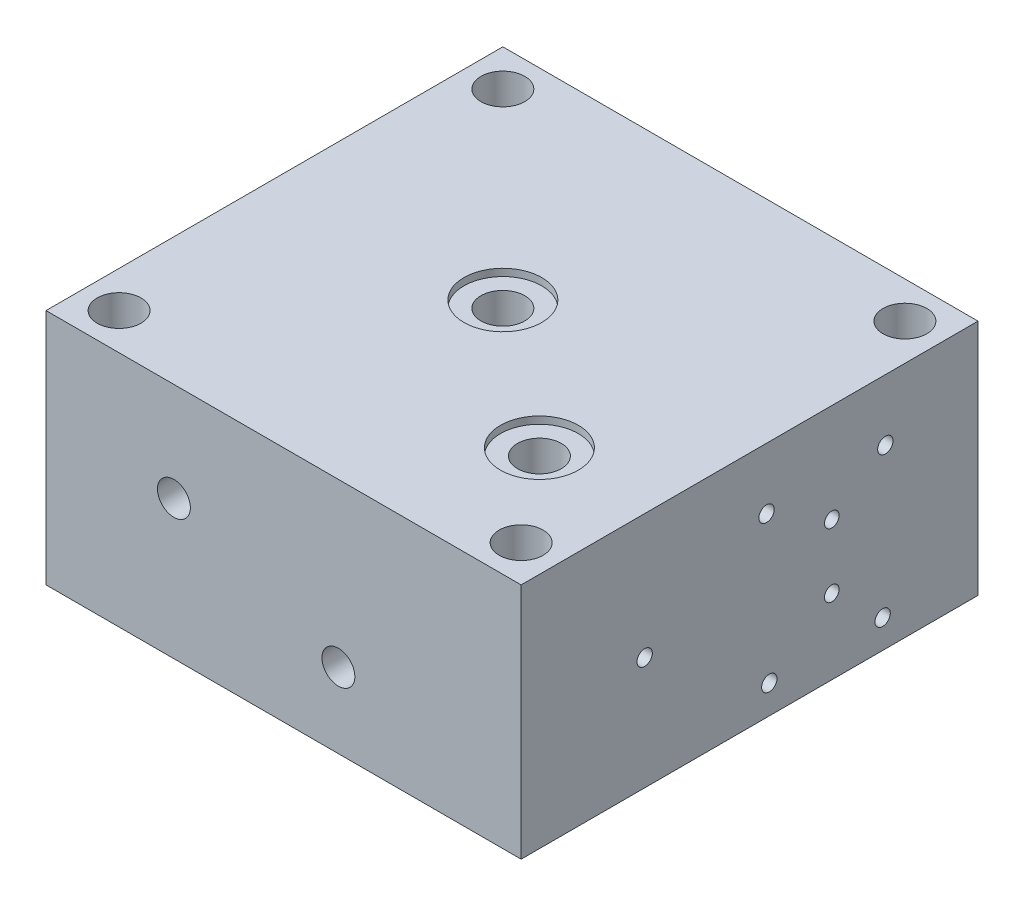
SolidWorks part; units mm, degrees
ref_plane "前视基准面" through (0, 0, 0) normal (0, 0, 1) x (1, 0, 0)
ref_plane "上视基准面" through (0, 0, 0) normal (0, 1, 0) x (1, 0, 0)
ref_plane "右视基准面" through (0, 0, 0) normal (1, 0, 0) x (0, 0, -1)
sketch "草图2" plane through (0, 0, 0) normal (0, 1, 0) x (1, 0, 0)
  line L1 (-65, -62.5) -> (65, -62.5)
  line L2 (-65, -62.5) -> (-65, 62.5)
  line L3 (-65, 62.5) -> (65, 62.5)
  line L4 (65, -62.5) -> (65, 62.5)
  line L5 (-65, -62.5) -> (65, 62.5) construction
  line L6 (-65, 62.5) -> (65, -62.5) construction
  circle A0 centre (-55, 52.5) radius 6
  circle A1 centre (55, 52.5) radius 6
  circle A2 centre (55, -52.5) radius 6
  circle A3 centre (-55, -52.5) radius 6
  point P0 (0, 0)
  dimension "D1" = 10
  dimension "D2" = 10
  dimension "D3" = 2
  dimension "D4" = 2
extrude "凸台-拉伸1" add sketch "草图2" along normal blind 65 contours A2 | A3 | A1 | L2 L3 L4 L1 | A0
sketch "草图19" plane through (-65, 0, 0) normal (-1, 0, 0) x (0, 0, 1)
  line L0 (-62.5, 65) -> (-62.5, 38)
  line L1 (-62.5, 65) -> (-62.5, 0) construction
  line L2 (-62.5, 38) -> (-22.5, 38)
sketch "草图21" plane through (0, 0, -62.5) normal (0, 0, -1) x (-1, 0, 0)
  point P10 (-4.7, 9.8)
  point P11 (-12.2, 20.5)
  point P12 (-30.5, 9.8)
  point P13 (-23, 20.5)
  point P22 (-30.5, 31.2)
  point P23 (-4.7, 31.2)
  point P24 (-32.5, 20.5)
  point P25 (-17.6, 30.4)
  dimension "D3" = 27.8
  dimension "D4" = 12.9
  dimension "D5" = 10.7
  dimension "D6" = 20.6
  dimension "D7" = 21.4
  dimension "D8" = 25.8
  dimension "D1" = 7.5
  dimension "D2" = 18.3
sketch "草图26" plane through (65, 0, 0) normal (1, 0, 0) x (0, 0, -1)
  point P2 (-28.7046, 20.5)
  point P8 (5.4, 7.8)
  point P9 (4.65, 48.3)
  point P10 (37.15, 48.3)
  point P11 (36.4, 7.8)
  point P12 (22.4954, 38)
  point P13 (22.4954, 20.5)
  dimension "D1" = 40.5
  dimension "D2" = 0.75
  dimension "D3" = 31
  dimension "D4" = 31.75
  dimension "D5" = 30.2
  dimension "D6" = 12.7
hole_wizard "M5 螺纹孔3" positions "3D草图11" profile "草图27" tap size "M5" standard "GB"
sketch3d "3D草图11"
  point P0 (65, 48.3, -4.65)
  point P3 (65, 48.3, -37.15)
  point P6 (65, 7.8, -36.4)
  point P9 (65, 7.8, -5.4)
sketch "草图27" plane through (65, 48.3, -4.65) normal (0, 1, 0) x (0, 0, -1)
  line L0 (0, 0) -> (0, 13.2618)
  line L1 (0, 13.2618) -> (2.1, 12)
  line L2 (2.1, 12) -> (2.1, 0)
  line L5 (2.1, 0) -> (0, 0)
  line L10 (0, 13.2618) -> (-2.1, 12) construction
  line L11 (0, -6.35) -> (0, 107.95) construction
  dimension "螺纹孔钻头直径" = 4.2
  dimension "螺纹孔钻头深度" = 12
  dimension "导头角度" = 118
cosmetic thread "孔螺蚊线9" parameters "D1"=8, "D2"=5
cosmetic thread "孔螺蚊线10" parameters "D1"=8, "D2"=5
cosmetic thread "孔螺蚊线11" parameters "D1"=8, "D2"=5
cosmetic thread "孔螺蚊线12" parameters "D1"=8, "D2"=5
hole_wizard "Ø4.0 (4) 直径孔9" positions "3D草图12" profile "草图28" hole size "Ø4.0" standard "GB"
sketch3d "3D草图12"
  point P0 (65, 20.5, -22.4954)
sketch "草图28" plane through (65, 20.5, -22.4954) normal (0, 1, 0) x (0, 0, -1)
  line L0 (0, 0) -> (0, 33.7017)
  line L1 (0, 33.7017) -> (2, 32.5)
  line L2 (2, 32.5) -> (2, 0)
  line L5 (2, 0) -> (0, 0)
  line L10 (0, 33.7017) -> (-2, 32.5) construction
  line L11 (0, -6.35) -> (0, 107.95) construction
  dimension "孔直径" = 4
  dimension "孔深度" = 32.5
  dimension "导头角度" = 118
hole_wizard "Ø6.0 (6) 直径孔1" positions "3D草图13" profile "草图31" hole size "Ø6.0" standard "GB"
sketch3d "3D草图13"
  point P0 (32.5, 20.5, -62.5)
sketch "草图31" plane through (32.5, 20.5, -62.5) normal (1, 0, 0) x (0, 1, 0)
  line L0 (0, 0) -> (0, 43.8026)
  line L1 (0, 43.8026) -> (3, 42)
  line L2 (3, 42) -> (3, 0)
  line L5 (3, 0) -> (0, 0)
  line L10 (0, 43.8026) -> (-3, 42) construction
  line L11 (0, -6.35) -> (0, 107.95) construction
  dimension "孔直径" = 6
  dimension "孔深度" = 42
  dimension "导头角度" = 118
sketch "草图38" plane through (-65, 0, 0) normal (-1, 0, 0) x (0, 0, 1)
  point P0 (-22.5, 38)
  point P1 (-37, 52.5)
  point P6 (-8, 52.5)
  point P7 (-8, 23.5)
  point P8 (-37, 23.5)
  dimension "D1" = 14.5
  dimension "D2" = 14.5
  dimension "D3" = 2
  dimension "D4" = 2
sketch "草图40" plane through (0, 0, 62.5) normal (0, 0, 1) x (1, 0, 0)
  line L0 (-65, 38) -> (-30, 38)
hole_wizard "Ø4.0 (4) 直径孔11" positions "3D草图17" profile "草图41" hole size "Ø4.0" standard "GB"
sketch3d "3D草图17"
  point P0 (-30, 38, 62.5)
sketch "草图41" plane through (-30, 38, 62.5) normal (1, 0, 0) x (0, -1, 0)
  line L0 (0, 0) -> (0, 86.2017)
  line L1 (0, 86.2017) -> (2, 85)
  line L2 (2, 85) -> (2, 0)
  line L5 (2, 0) -> (0, 0)
  line L10 (0, 86.2017) -> (-2, 85) construction
  line L11 (0, -6.35) -> (0, 107.95) construction
  dimension "孔直径" = 4
  dimension "孔深度" = 85
  dimension "导头角度" = 118
hole_wizard "M10x1.0 螺纹孔1" positions "3D草图18" profile "草图42" tap size "M10x1.0" standard "GB"
sketch3d "3D草图18"
  point P0 (-30, 38, 62.5)
sketch "草图42" plane through (-30, 38, 62.5) normal (1, 0, 0) x (0, -1, 0)
  line L0 (0, 0) -> (0, 15.7039)
  line L1 (0, 15.7039) -> (4.5, 13)
  line L2 (4.5, 13) -> (4.5, 0)
  line L5 (4.5, 0) -> (0, 0)
  line L10 (0, 15.7039) -> (-4.5, 13) construction
  line L11 (0, -6.35) -> (0, 107.95) construction
  dimension "螺纹孔钻头直径" = 9
  dimension "螺纹孔钻头深度" = 13
  dimension "导头角度" = 118
cosmetic thread "孔螺蚊线17" parameters "D1"=8, "D2"=10
sketch "草图44" plane through (0, 0, 62.5) normal (0, 0, 1) x (1, 0, 0)
  line L0 (65, 0) -> (17.6, 0)
  line L1 (-65, 0) -> (65, 0) construction
  line L2 (17.6, 0) -> (17.6, 30.4)
sketch "草图46" plane through (0, 65, 0) normal (0, 1, 0) x (1, 0, 0)
  line L0 (65, -62.5) -> (35, -62.5)
  line L1 (65, -62.5) -> (17.6, -62.5) construction
  line L2 (35, -62.5) -> (35, -27.5)
  line L3 (65, 62.5) -> (-5, 62.5)
  line L4 (-65, 62.5) -> (65, 62.5) construction
  line L5 (-5, 62.5) -> (-5, -7.5)
sketch "草图50" plane through (0, 0, 0) normal (0, -1, 0) x (-1, 0, 0)
  line L0 (65, 62.5) -> (-23, 62.5)
  line L1 (65, 62.5) -> (-65, 62.5) construction
  line L2 (-23, 62.5) -> (-23, 3.7)
sketch "草图52" plane through (0, 0, -62.5) normal (0, 0, -1) x (-1, 0, 0)
  line L0 (-32.5, 20.5) -> (-23.7, 20.5)
  line L1 (-23.7, 20.5) -> (-23.7, 10.1)
  line L2 (-23.7, 20.5) -> (-23.7, 30.9)
  line L3 (-23.7, 20.5) -> (-15, 20.5)
  line L4 (-32.5, 20.5) -> (-32.5, 36)
  line L5 (-32.5, 36) -> (-45.2, 36)
  line L6 (-45.2, 36) -> (-4.7, 36)
  line L8 (-4.7, 36) -> (-4.7, 5)
  line L9 (-45.2, 36) -> (-45.2, 5)
  point P4 (0, 0)
hole_wizard "M5 螺纹孔5" positions "3D草图25" profile "草图53" tap size "M5" standard "GB"
sketch3d "3D草图25"
  point P0 (4.7, 36, -62.5)
  point P3 (45.2, 36, -62.5)
  point P6 (45.2, 5, -62.5)
  point P9 (4.7, 5, -62.5)
sketch "草图53" plane through (4.7, 36, -62.5) normal (1, 0, 0) x (0, 1, 0)
  line L0 (0, 0) -> (0, 11.2618)
  line L1 (0, 11.2618) -> (2.1, 10)
  line L2 (2.1, 10) -> (2.1, 0)
  line L5 (2.1, 0) -> (0, 0)
  line L10 (0, 11.2618) -> (-2.1, 10) construction
  line L11 (0, -6.35) -> (0, 107.95) construction
  dimension "螺纹孔钻头直径" = 4.2
  dimension "螺纹孔钻头深度" = 10
  dimension "导头角度" = 118
cosmetic thread "孔螺蚊线25" parameters "D1"=8, "D2"=5
cosmetic thread "孔螺蚊线26" parameters "D1"=8, "D2"=5
cosmetic thread "孔螺蚊线27" parameters "D1"=8, "D2"=5
cosmetic thread "孔螺蚊线28" parameters "D1"=8, "D2"=5
hole_wizard "Ø6.0 (6) 直径孔2" positions "3D草图26" profile "草图54" hole size "Ø6.0" standard "GB"
sketch3d "3D草图26"
  point P0 (23.7, 10.1, -62.5)
sketch "草图54" plane through (23.7, 10.1, -62.5) normal (1, 0, 0) x (0, 1, 0)
  line L0 (0, 0) -> (0, 61.8026)
  line L1 (0, 61.8026) -> (3, 60)
  line L2 (3, 60) -> (3, 0)
  line L5 (3, 0) -> (0, 0)
  line L10 (0, 61.8026) -> (-3, 60) construction
  line L11 (0, -6.35) -> (0, 107.95) construction
  dimension "孔直径" = 6
  dimension "孔深度" = 60
  dimension "导头角度" = 118
hole_wizard "Ø6.0 (6) 直径孔3" positions "3D草图27" profile "草图55" hole size "Ø6.0" standard "GB"
sketch3d "3D草图27"
  point P0 (23.7, 30.9, -62.5)
sketch "草图55" plane through (23.7, 30.9, -62.5) normal (1, 0, 0) x (0, 1, 0)
  line L0 (0, 0) -> (0, 91.8026)
  line L1 (0, 91.8026) -> (3, 90)
  line L2 (3, 90) -> (3, 0)
  line L5 (3, 0) -> (0, 0)
  line L10 (0, 91.8026) -> (-3, 90) construction
  line L11 (0, -6.35) -> (0, 107.95) construction
  dimension "孔直径" = 6
  dimension "孔深度" = 90
  dimension "导头角度" = 118
sketch "草图56" plane through (65, 0, 0) normal (1, 0, 0) x (0, 0, -1)
  line L1 (62.5, 0) -> (-28.7046, 0)
  line L2 (-62.5, 0) -> (62.5, 0) construction
  line L3 (-28.7046, 0) -> (-28.7046, 30.9)
hole_wizard "M5 螺纹孔8" positions "3D草图30" profile "草图61" tap size "M5" standard "GB"
sketch3d "3D草图30"
  point P0 (65, 30.9, 28.7046)
sketch "草图61" plane through (65, 30.9, 28.7046) normal (0, 1, 0) x (0, 0, -1)
  line L0 (0, 0) -> (0, 42.5718)
  line L1 (0, 42.5718) -> (2.1, 41.31)
  line L2 (2.1, 41.31) -> (2.1, 0)
  line L5 (2.1, 0) -> (0, 0)
  line L10 (0, 42.5718) -> (-2.1, 41.31) construction
  line L11 (0, -6.35) -> (0, 107.95) construction
  dimension "螺纹孔钻头直径" = 4.2
  dimension "螺纹孔钻头深度" = 41.31
  dimension "导头角度" = 118
cosmetic thread "孔螺蚊线31" parameters "D1"=10, "D2"=5
hole_wizard "Ø6.0 (6) 直径孔4" positions "3D草图31" profile "草图62" hole size "Ø6.0" standard "GB" end condition through all
sketch3d "3D草图31"
  point P0 (15, 20.5, -62.5)
sketch "草图62" plane through (15, 20.5, -62.5) normal (1, 0, 0) x (0, 1, 0)
  line L0 (0, 0) -> (0, 125)
  line L1 (0, 125) -> (3, 125)
  line L2 (3, 125) -> (3, 0)
  line L5 (3, 0) -> (0, 0)
  line L11 (0, -6.35) -> (0, 107.95) construction
  dimension "通孔孔直径" = 6
  dimension "通孔孔深度" = 125
sketch "草图65" plane through (0, 0, 62.5) normal (0, 0, 1) x (1, 0, 0)
  line L0 (65, 0) -> (15, 0)
  line L1 (-65, 0) -> (65, 0) construction
  line L2 (15, 0) -> (15, 20.5)
hole_wizard "M10x1.0 螺纹孔2" positions "3D草图32" profile "草图66" tap size "M10x1.0" standard "GB"
sketch3d "3D草图32"
  point P0 (15, 20.5, 62.5)
sketch "草图66" plane through (15, 20.5, 62.5) normal (1, 0, 0) x (0, -1, 0)
  line L0 (0, 0) -> (0, 15.7039)
  line L1 (0, 15.7039) -> (4.5, 13)
  line L2 (4.5, 13) -> (4.5, 0)
  line L5 (4.5, 0) -> (0, 0)
  line L10 (0, 15.7039) -> (-4.5, 13) construction
  line L11 (0, -6.35) -> (0, 107.95) construction
  dimension "螺纹孔钻头直径" = 9
  dimension "螺纹孔钻头深度" = 13
  dimension "导头角度" = 118
cosmetic thread "孔螺蚊线32" parameters "D1"=8, "D2"=10
sketch "草图70" plane through (65, 0, 0) normal (1, 0, 0) x (0, 0, -1)
  line L0 (62.5, 9.8) -> (2.5, 10.1)
  line L1 (2.5, 13.1) -> (2.5, 7.1) construction
sketch "草图73" plane through (0, 65, 0) normal (0, 1, 0) x (1, 0, 0)
  line L0 (-65, -62.5) -> (65, -62.5) construction
  line L2 (65, -62.5) -> (65, 62.5) construction
  circle A0 centre (-5, 2.5) radius 10.65
  dimension "D1" = 65
  dimension "D2" = 70
extrude "切除-拉伸1" cut sketch "草图73" against normal blind 1.97 contours A0
sketch "草图74" plane through (0, 63.03, 0) normal (0, 1, 0) x (1, 0, 0)
  circle A0 centre (-5, 2.5) radius 6
extrude "切除-拉伸2" cut sketch "草图74" against normal through all contours A0
sketch "草图75" plane through (0, 65, 0) normal (0, 1, 0) x (1, 0, 0)
  line L0 (-65, -62.5) -> (65, -62.5) construction
  line L2 (65, -62.5) -> (65, 62.5) construction
  circle A0 centre (35, -27.5) radius 10.65
  dimension "D1" = 35
  dimension "D2" = 30
extrude "切除-拉伸3" cut sketch "草图75" against normal blind 1.97
sketch "草图76" plane through (0, 63.03, 0) normal (0, 1, 0) x (1, 0, 0)
  line L0 (65, -62.5) -> (65, 62.5) construction
  line L1 (-65, -62.5) -> (65, -62.5) construction
  circle A0 centre (35, -27.5) radius 6
  dimension "D1" = 30
  dimension "D2" = 35
sketch "草图77" plane through (0, 63.03, 0) normal (0, 1, 0) x (1, 0, 0)
extrude "切除-拉伸4" cut sketch "草图76" against normal through all contours A0
sketch "草图78" plane through (0, 0, -62.5) normal (0, 0, -1) x (-1, 0, 0)
  line L0 (-23.9571, 0) -> (-24.0244, 0)
  line L1 (65, 0) -> (-65, 0) construction
sketch "草图82" plane through (65, 0, 0) normal (1, 0, 0) x (0, 0, -1)
  line L0 (-62.5, 65) -> (62.5, 65) construction
  line L1 (62.5, 65) -> (62.5, 0) construction
  circle A0 centre (22.5, 38) radius 2
  dimension "D1" = 27
  dimension "D2" = 40
extrude "切除-拉伸6" cut sketch "草图82" against normal blind 97
sketch "草图83" plane through (0, 0, 0) normal (0, -1, 0) x (-1, 0, 0)
  line L0 (-65, -62.5) -> (-65, 62.5) construction
  line L2 (65, 62.5) -> (-65, 62.5) construction
  circle A0 centre (-23, 3.7) radius 6
  dimension "D1" = 42
  dimension "D2" = 58.8
extrude "切除-拉伸7" cut sketch "草图83" against normal blind 13
